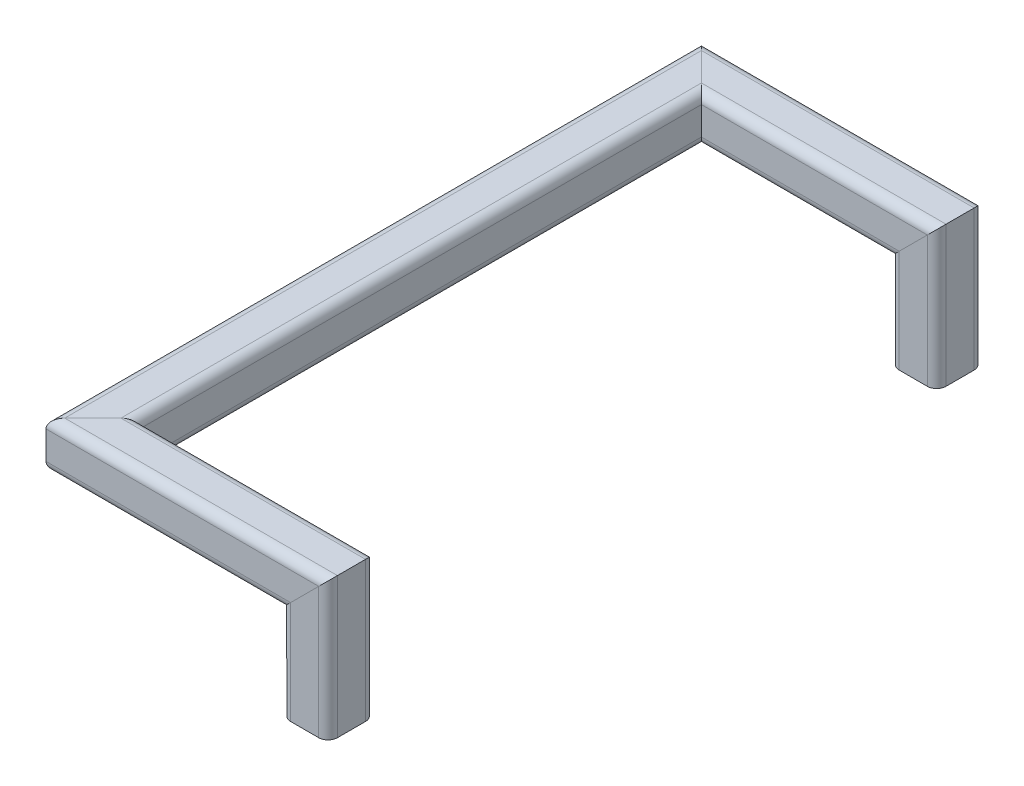
SolidWorks part; units mm, degrees
material "Plain Carbon Steel"
ref_plane "Front" through (0, 0, 0) normal (0, 0, 1) x (1, 0, 0)
ref_plane "Top" through (0, 0, 0) normal (0, 1, 0) x (1, 0, 0)
ref_plane "Right" through (0, 0, 0) normal (1, 0, 0) x (0, 0, -1)
sketch3d "3DSketch1"
  line L0 (0, 0, 0) -> (127.635, 0, 0)
  line L1 (0, 0, 0) -> (0, 0, -330.2)
  line L2 (0, 0, -330.2) -> (127.635, 0, -330.2)
  line L3 (127.635, 0, 0) -> (127.635, -63.5, 0)
  line L4 (127.635, 0, -330.2) -> (127.635, -63.5, -330.2)
  dimension "D1" = 63.5
  dimension "D3" = 63.5
  dimension "D4" = 127.635
  dimension "D5" = 330.2
  dimension "D6" = 127.635
other "Square tubing 1 X 1 X 0.125(1)"
ref_plane "Plane2" through (0, 0, 0) normal (1, 0, 0) x (0, 0, -1)
sketch "Sketch1" plane through (0, 0, 0) normal (1, 0, 0) x (0, 0, -1)
  line L0 (-7.62, -9.525) -> (7.62, -9.525)
  line L1 (-9.525, -7.62) -> (-9.525, 7.62)
  line L2 (7.62, 9.525) -> (-7.62, 9.525)
  line L3 (9.525, 7.62) -> (9.525, -7.62)
  line L4 (-7.62, -12.7) -> (7.62, -12.7)
  line L5 (-12.7, -7.62) -> (-12.7, 7.62)
  line L6 (7.62, 12.7) -> (-7.62, 12.7)
  line L7 (12.7, 7.62) -> (12.7, -7.62)
  line L8 (0, 0) -> (9.525, 0) construction
  line L9 (0, 0) -> (0, 9.525) construction
  arc A0 (12.7, 7.62) -> (7.62, 12.7) centre (7.62, 7.62) ccw
  arc A1 (7.62, -12.7) -> (12.7, -7.62) centre (7.62, -7.62) ccw
  arc A2 (-12.7, -7.62) -> (-7.62, -12.7) centre (-7.62, -7.62) ccw
  arc A3 (-7.62, 12.7) -> (-12.7, 7.62) centre (-7.62, 7.62) ccw
  arc A4 (-7.62, 9.525) -> (-9.525, 7.62) centre (-7.62, 7.62) ccw
  arc A5 (9.525, 7.62) -> (7.62, 9.525) centre (7.62, 7.62) ccw
  arc A6 (7.62, -9.525) -> (9.525, -7.62) centre (7.62, -7.62) ccw
  arc A7 (-9.525, -7.62) -> (-7.62, -9.525) centre (-7.62, -7.62) ccw
  point P3 (0, 12.7)
  point P4 (12.7, 0)
  point P5 (0, -12.7)
  point P6 (-12.7, 0)
  point P7 (-12.7, 12.7)
  point P8 (-12.7, -12.7)
  point P33 (0, 0)
  point P35 (12.7, -12.7)
  point P36 (12.7, 12.7)
  point P37 (0, 0)
  dimension "D1" = 5.08
  dimension "Thickness" = 3.175
  dimension "V_leg" = 25.4
equation "\"Total Cutting Length\"= \"Cutting Length-Outer\" + \"Cutting Length-Inner\""
equation "\"Amount in ft^2\"= \"Bounding Box Area-Blank\" / 144"
